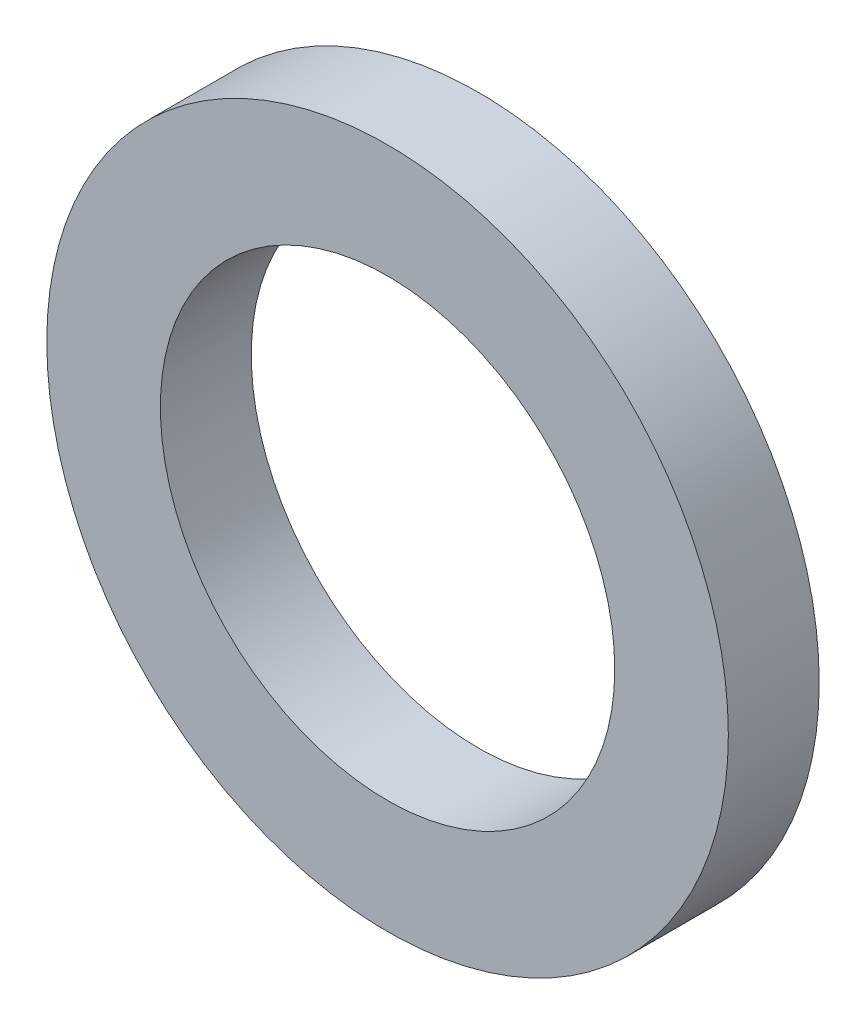
SolidWorks part; units mm, degrees
ref_plane "Alzado" through (0, 0, 0) normal (0, 0, 1) x (1, 0, 0)
ref_plane "Planta" through (0, 0, 0) normal (0, 1, 0) x (1, 0, 0)
ref_plane "Vista lateral" through (0, 0, 0) normal (1, 0, 0) x (0, 0, -1)
sketch "Croquis1" plane through (0, 0, 0) normal (0, 0, 1) x (1, 0, 0)
  circle A0 centre (0, 0) radius 0.5
  circle A1 centre (0, 0) radius 0.75
  dimension "D1" = 1
  dimension "D2" = 1.5
extrude "Saliente-Extruir1" add sketch "Croquis1" along normal blind 0.2
